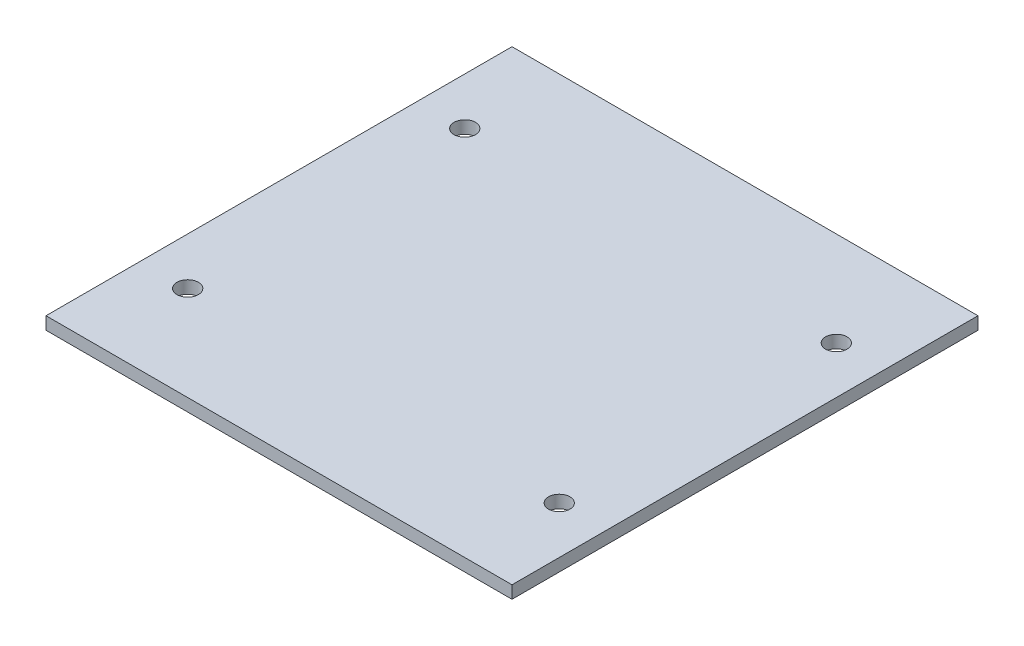
SolidWorks part; units mm, degrees
ref_plane "Front Plane" through (0, 0, 0) normal (0, 0, 1) x (1, 0, 0)
ref_plane "Top Plane" through (0, 0, 0) normal (0, 1, 0) x (1, 0, 0)
ref_plane "Right Plane" through (0, 0, 0) normal (1, 0, 0) x (0, 0, -1)
sketch "Sketch1" plane through (0, 0, 0) normal (0, 1, 0) x (1, 0, 0)
  line L1 (-37, 37) -> (37, 37)
  line L2 (-37, 37) -> (-37, -37)
  line L3 (-37, -37) -> (37, -37)
  line L4 (37, 37) -> (37, -37)
  line L5 (-37, 37) -> (37, -37) construction
  line L6 (-37, -37) -> (37, 37) construction
  point P0 (0, 0)
  dimension "D1" = 74
  dimension "D2" = 74
extrude "Extrude1" add sketch "Sketch1" along normal blind 2
sketch "Sketch2" plane through (0, 2, 0) normal (0, 1, 0) x (1, 0, 0)
  line L0 (37, 37) -> (-37, 37) construction
  line L1 (-37, 37) -> (-37, -37) construction
  line L2 (37, -37) -> (37, 37) construction
  line L3 (-37, -37) -> (37, -37) construction
  circle A0 centre (29.5, 22) radius 1.7
  circle A1 centre (-29.5, 22) radius 1.7
  circle A2 centre (-29.5, -22) radius 1.7
  circle A3 centre (29.5, -22) radius 1.7
  dimension "D1" = 15
  dimension "D2" = 7.5
  dimension "D3" = 15
  dimension "D4" = 7.5
  dimension "D5" = 7.5
  dimension "D6" = 15
  dimension "D7" = 15
  dimension "D8" = 7.5
  dimension "D9" = 3.4
extrude "Extrude2" cut sketch "Sketch2" against normal blind 2
